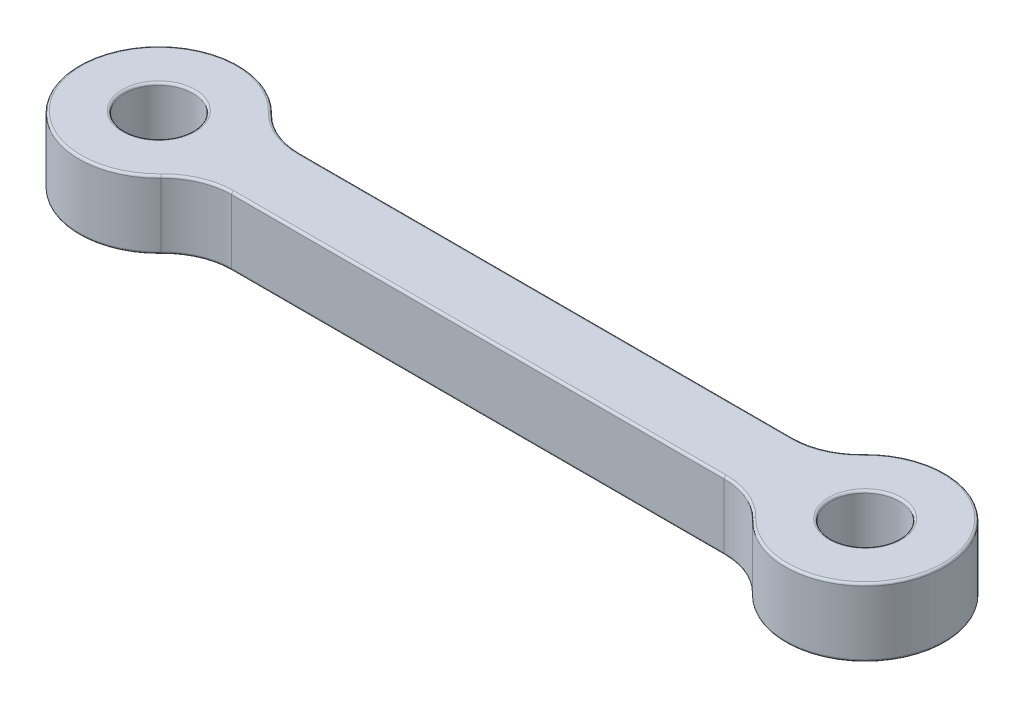
SolidWorks part; units mm, degrees
ref_plane "Front Plane" through (0, 0, 0) normal (0, 0, 1) x (1, 0, 0)
ref_plane "Top Plane" through (0, 0, 0) normal (0, 1, 0) x (1, 0, 0)
ref_plane "Right Plane" through (0, 0, 0) normal (1, 0, 0) x (0, 0, -1)
sketch "Sketch1" plane through (0, 0, 0) normal (0, 1, 0) x (1, 0, 0)
  line L0 (0, 0) -> (1.5, 0)
  line L1 (4.6904, 1.5) -> (26.3096, 1.5)
  line L2 (4.6904, -1.5) -> (26.3096, -1.5)
  line L3 (0, 1.5) -> (31, 1.5) construction
  line L5 (0, 0) -> (31, 0) construction
  line L6 (0, -1.5) -> (31, -1.5) construction
  arc A0 (2.5256, 2.4231) -> (2.5256, -2.4231) centre (0, 0) ccw
  circle A1 centre (0, 0) radius 1.5
  circle A2 centre (31, 0) radius 1.5
  arc A3 (28.4744, -2.4231) -> (28.4744, 2.4231) centre (31, 0) ccw
  arc A4 (28.4744, -2.4231) -> (26.3096, -1.5) centre (26.3096, -4.5) ccw
  arc A5 (26.3096, 1.5) -> (28.4744, 2.4231) centre (26.3096, 4.5) ccw
  arc A6 (4.6904, -1.5) -> (2.5256, -2.4231) centre (4.6904, -4.5) ccw
  arc A7 (4.6904, 1.5) -> (2.5256, 2.4231) centre (4.6904, 4.5) cw
  dimension "D1" = 7
  dimension "D2" = 3
  dimension "D4" = 7
  dimension "D5" = 3
  dimension "D8" = 3
  dimension "D3" = 31
  dimension "D6" = 1.5
  dimension "D7" = 1.5
extrude "Boss-Extrude1" add sketch "Sketch1" along normal blind 3 contours L1 A7 A0 A6 L2 A4 A3 A5 A1 A2
fillet "Fillet1" radius 0.1 20 edges at (3.5137, 0, -1.7404) (-3.5, 0, 0) (3.5137, 0, 1.7404) (15.5, 0, 1.5) (27.4863, 0, 1.7404) (34.5, 0, 0) (27.4863, 0, -1.7404) (15.5, 0, -1.5) (31, 0, 1.5) (0, 0, 1.5) (27.4863, 3, -1.7404) (34.5, 3, 0) (27.4863, 3, 1.7404) (15.5, 3, 1.5) (3.5137, 3, 1.7404) (-3.5, 3, 0) (3.5137, 3, -1.7404) (15.5, 3, -1.5) (31, 3, 1.5) (0, 3, 1.5)
scale "Scale1" scale about centroid uniform scaling yes scale factor 1.8
